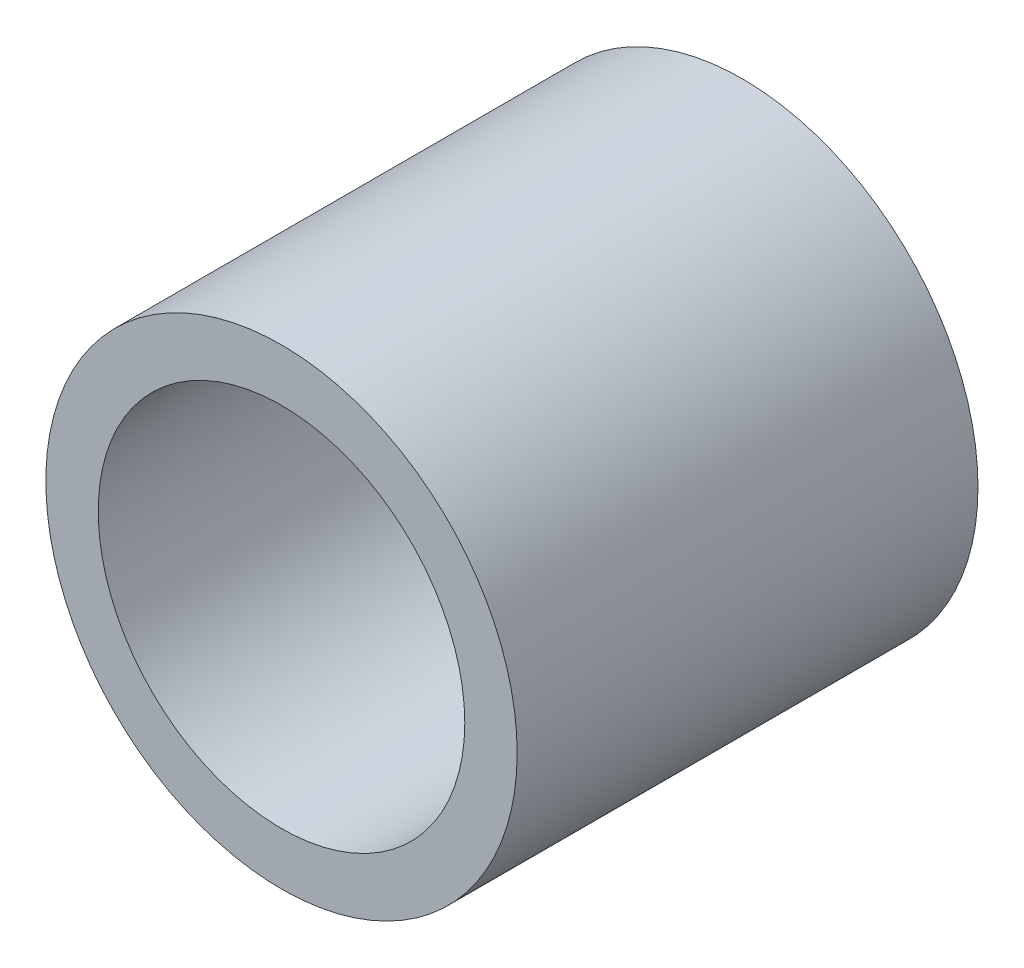
SolidWorks part; units mm, degrees
ref_plane "Plan de face" through (0, 0, 0) normal (0, 0, 1) x (1, 0, 0)
ref_plane "Plan de dessus" through (0, 0, 0) normal (0, 1, 0) x (1, 0, 0)
ref_plane "Plan de droite" through (0, 0, 0) normal (1, 0, 0) x (0, 0, -1)
sketch "Esquisse1" plane through (0, 0, 0) normal (0, 0, 1) x (1, 0, 0)
  circle A0 centre (0, 0) radius 4.375
  circle A1 centre (0, 0) radius 5.625
  dimension "D1" = 8.75
  dimension "D2" = 11.25
extrude "Extrusion1" add sketch "Esquisse1" along normal blind 11
